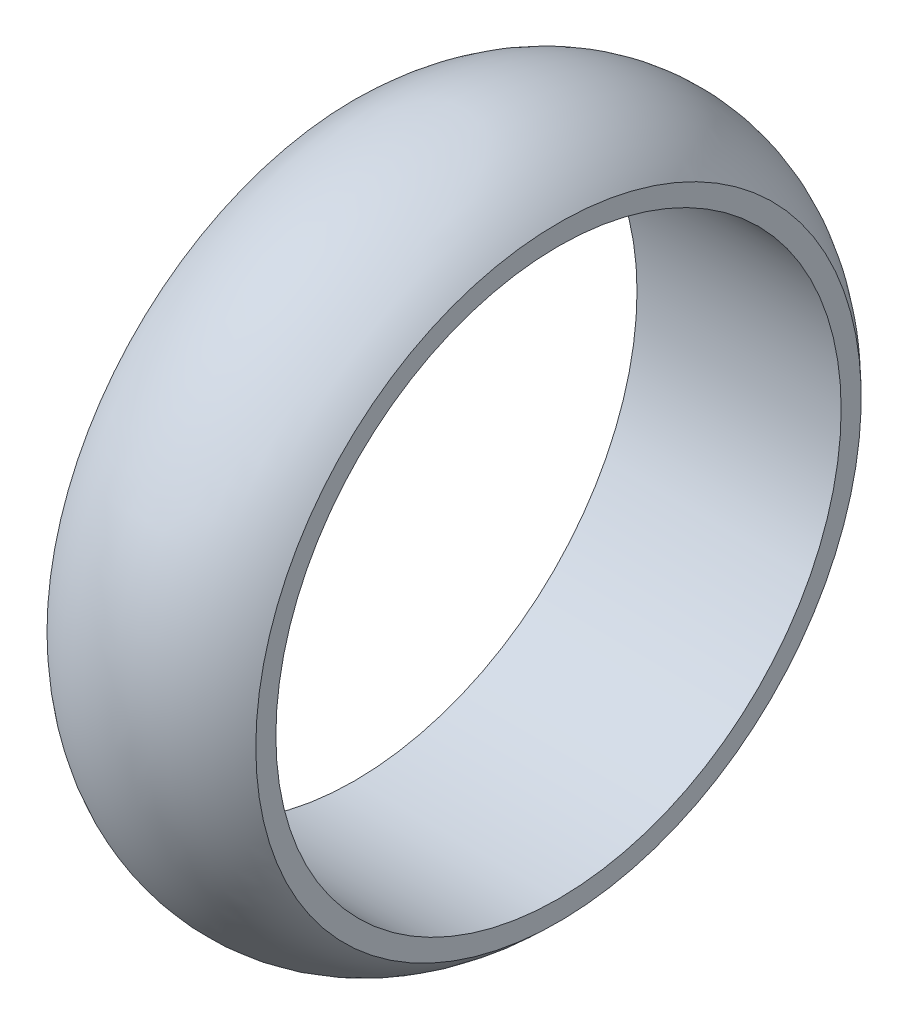
SolidWorks part; units mm, degrees
material "POLIURETANO (11671)"
ref_plane "Alzado" through (0, 0, 0) normal (0, 0, 1) x (1, 0, 0)
ref_plane "Planta" through (0, 0, 0) normal (0, 1, 0) x (1, 0, 0)
ref_plane "Vista lateral" through (0, 0, 0) normal (1, 0, 0) x (0, 0, -1)
sketch "Croquis1" plane through (0, 0, 0) normal (0, 0, 1) x (1, 0, 0)
  line L0 (-82.55, 228.6) -> (82.55, 228.6) construction
  line L1 (0, 228.6) -> (0, 0) construction
  line L2 (-74.2081, 0) -> (77.194, 0) construction
  line L3 (-82.55, 228.6) -> (-82.55, 248.6)
  line L4 (82.55, 228.6) -> (82.55, 244.8291)
  line L5 (-82.55, 228.6) -> (82.55, 228.6)
  arc A0 (82.55, 244.8291) -> (-82.55, 248.6) centre (-1.8845, 164.2076) ccw
  point P4 (0, 228.6)
  dimension "D1" = 165.1
  dimension "D2" = 20
  dimension "D3" = 228.6
revolve "Revolución1" add sketch "Croquis1" angle 360 about L2
